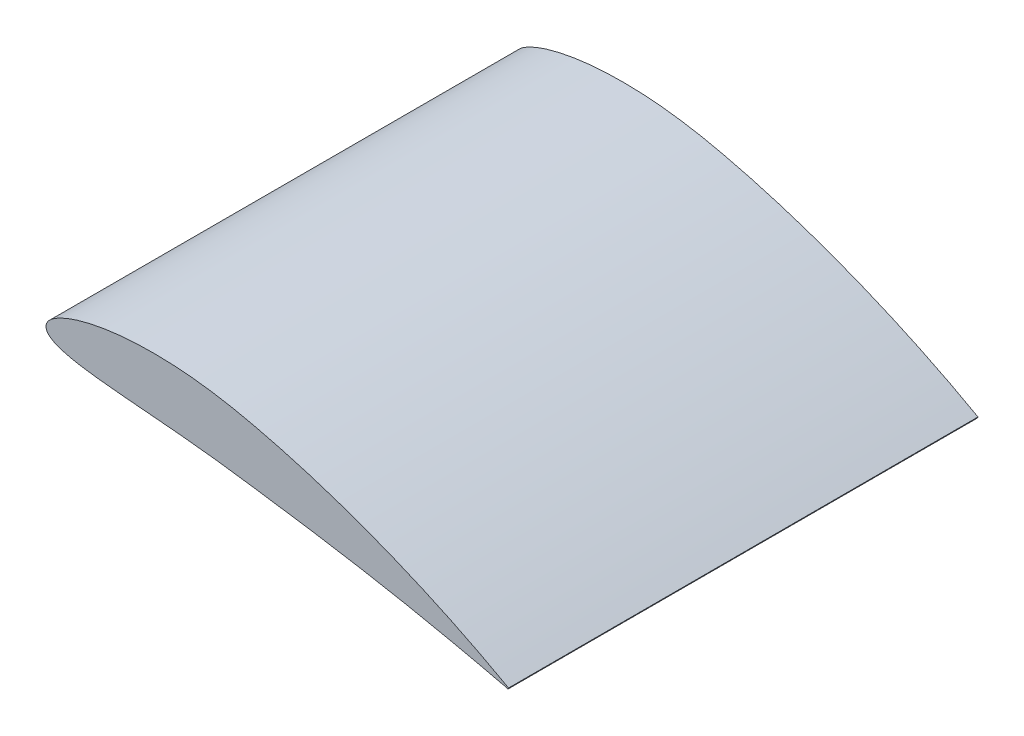
SolidWorks part; units mm, degrees
ref_plane "Front Plane" through (0, 0, 0) normal (0, 0, 1) x (1, 0, 0)
ref_plane "Top Plane" through (0, 0, 0) normal (0, 1, 0) x (1, 0, 0)
ref_plane "Right Plane" through (0, 0, 0) normal (1, 0, 0) x (0, 0, -1)
curve "Curve1"
  spline degree 3 poles (1.0003, 0.0012, 0) (0.9994, 0.0015, 0) (0.9958, 0.0028, 0) (0.9879, 0.0055, 0) (0.9747, 0.0099, 0) (0.9565, 0.0159, 0) (0.9333, 0.0233, 0) (0.9054, 0.0318, 0) (0.8731, 0.0411, 0) (0.8366, 0.051, 0) (0.7964, 0.0612, 0) (0.7528, 0.0713, 0) (0.7063, 0.0811, 0) (0.6574, 0.0903, 0) (0.6067, 0.0985, 0) (0.5546, 0.1057, 0) (0.5018, 0.1115, 0) (0.4488, 0.1158, 0) (0.3959, 0.1186, 0) (0.3436, 0.1189, 0) (0.2927, 0.1164, 0) (0.2442, 0.1112, 0) (0.1988, 0.1037, 0) (0.157, 0.0942, 0) (0.1194, 0.0831, 0) (0.0865, 0.0711, 0) (0.0585, 0.0584, 0) (0.0357, 0.0457, 0) (0.0184, 0.0334, 0) (0.0064, 0.0218, 0) (-0.0005, 0.0108, 0) (-0.0011, -0.0003, 0) (0.0055, -0.0092, 0) (0.017, -0.0148, 0) (0.0329, -0.0185, 0) (0.0533, -0.0204, 0) (0.0781, -0.0208, 0) (0.107, -0.0198, 0) (0.1398, -0.0176, 0) (0.176, -0.0147, 0) (0.2153, -0.0111, 0) (0.2574, -0.0074, 0) (0.3019, -0.0037, 0) (0.3484, -0.0005, 0) (0.397, 0.002, 0) (0.4471, 0.0037, 0) (0.4983, 0.0055, 0) (0.5496, 0.0069, 0) (0.6006, 0.0079, 0) (0.6505, 0.0085, 0) (0.699, 0.0086, 0) (0.7455, 0.0083, 0) (0.7894, 0.0076, 0) (0.8302, 0.0065, 0) (0.8675, 0.0053, 0) (0.9007, 0.0039, 0) (0.9296, 0.0027, 0) (0.9539, 0.0013, 0) (0.9727, 0.0006, 0) (0.9872, -0.0011, 0) (0.9944, 0, 0) (0.9999, -0.002, 0) (1, -0.0005, 0) (1, 0, 0) knots 0 0 0 0 0.001372 0.005465 0.012235 0.021602 0.033461 0.047671 0.064081 0.082496 0.102719 0.124527 0.147676 0.171913 0.196978 0.222597 0.248497 0.274385 0.300041 0.32569 0.350525 0.37428 0.396711 0.417577 0.436654 0.453744 0.46868 0.481329 0.491631 0.499616 0.505546 0.510185 0.514824 0.520702 0.528516 0.538466 0.550543 0.564643 0.580638 0.598345 0.617584 0.638174 0.659922 0.682632 0.706121 0.730727 0.7557 0.780732 0.805564 0.829932 0.85357 0.876213 0.89761 0.917519 0.935698 0.951943 0.966047 0.97784 0.987174 0.993932 0.998018 0.999386 1 1 1 1
sketch "Sketch2" plane through (0, 0, 0) normal (0, 0, 1) x (1, 0, 0)
  line L0 (0.9853, -0.1725) -> (0.9848, -0.1736)
  spline S1 degree 3 poles (0.9853, -0.1725) (0.9844, -0.172) (0.9812, -0.1702) (0.9738, -0.1661) (0.9616, -0.1595) (0.9361, -0.1458) (0.8932, -0.1237) (0.843, -0.0996) (0.7949, -0.078) (0.7384, -0.054) (0.6781, -0.0305) (0.5978, -0.0024) (0.5305, 0.0182) (0.4621, 0.0361) (0.4105, 0.048) (0.359, 0.0574) (0.3085, 0.0638) (0.2598, 0.0671) (0.2138, 0.0676) (0.171, 0.0655) (0.132, 0.0611) (0.0975, 0.055) (0.0677, 0.0474) (0.0431, 0.0388) (0.0239, 0.0297) (0.0101, 0.0204) (0.0014, 0.0107) (-0.0011, -0.0001) (0.0038, -0.01) (0.0142, -0.0175) (0.0292, -0.0239) (0.049, -0.0293) (0.0733, -0.034) (0.102, -0.0381) (0.1346, -0.0417) (0.1708, -0.045) (0.2101, -0.0483) (0.2678, -0.0533) (0.3283, -0.0591) (0.3913, -0.067) (0.441, -0.074) (0.4917, -0.0811) (0.559, -0.0911) (0.6254, -0.1017) (0.6899, -0.1129) (0.7356, -0.1213) (0.7787, -0.1296) (0.8187, -0.1378) (0.8552, -0.1454) (0.8877, -0.1525) (0.9159, -0.1588) (0.9396, -0.1644) (0.958, -0.1683) (0.972, -0.1725) (0.9792, -0.1727) (0.9843, -0.1756) (0.9847, -0.1741) (0.9848, -0.1736) knots 0 0 0 0 0.001372 0.005465 0.012235 0.021602 0.047671 0.082496 0.102719 0.124527 0.171913 0.196978 0.248497 0.274385 0.300041 0.32569 0.350525 0.37428 0.396711 0.417577 0.436654 0.453744 0.46868 0.481329 0.491631 0.499616 0.505546 0.510185 0.514824 0.520702 0.528516 0.538466 0.550543 0.564643 0.580638 0.598345 0.617584 0.638174 0.682632 0.706121 0.730727 0.7557 0.780732 0.829932 0.85357 0.876213 0.89761 0.917519 0.935698 0.951943 0.966047 0.97784 0.987174 0.993932 0.998018 0.999386 1 1 1 1
extrude "Boss-Extrude1" add sketch "Sketch2" along normal blind 1
